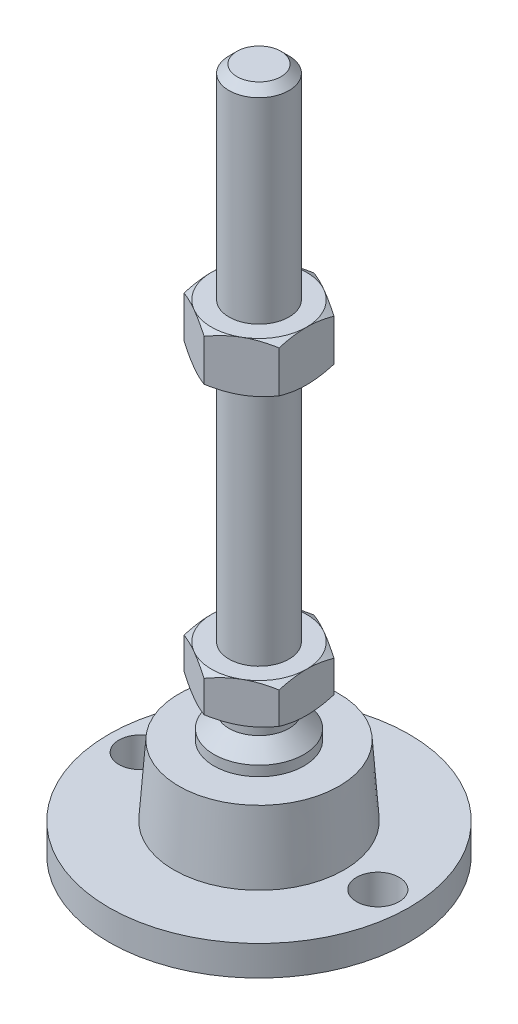
SolidWorks part; units mm, degrees
ref_plane "Спереди" through (0, 0, 0) normal (0, 0, 1) x (1, 0, 0)
ref_plane "Сверху" through (0, 0, 0) normal (0, 1, 0) x (1, 0, 0)
ref_plane "Справа" through (0, 0, 0) normal (1, 0, 0) x (0, 0, -1)
sketch "Эскиз1" plane through (0, 0, 0) normal (0, 0, 1) x (1, 0, 0)
  line L0 (0, 0) -> (-30, 0)
  line L3 (-30, 0) -> (-30, 6)
  line L12 (-6, 37) -> (-6, 135.4)
  line L13 (-6, 135.4) -> (-4.4, 137)
  line L14 (-4.4, 137) -> (0, 137)
  line L15 (0, 137) -> (0, 0) construction
  line L16 (-30, 6) -> (-17, 6)
  line L17 (0, 0) -> (0, 137)
  line L18 (0, 0) -> (0, -7.9595) construction
  line L19 (-6, 37) -> (-6, 29)
  line L21 (-9, 20) -> (-16, 20)
  line L22 (-17, 6) -> (-16, 20)
  line L23 (-9, 20) -> (-9, 22)
  line L24 (-9, 22) -> (-6, 25)
  line L25 (-6, 25) -> (-6, 29)
  line L26 (-6, 37) -> (0, 37) construction
  point P8 (-6, 86.2)
revolve "Повернуть1" add sketch "Эскиз1" angle 360 about L17
ref_plane "Плоскость2" through (0, 29, 0) normal (0, 1, 0) x (1, 0, 0)
sketch "Эскиз2" plane through (0, 29, 0) normal (0, 1, 0) x (1, 0, 0)
  line L1 (0, 10.9697) -> (-9.5, 5.4848)
  line L2 (-9.5, 5.4848) -> (-9.5, -5.4848)
  line L3 (-9.5, -5.4848) -> (0, -10.9697)
  line L4 (0, -10.9697) -> (9.5, -5.4848)
  line L5 (9.5, -5.4848) -> (9.5, 5.4848)
  line L6 (9.5, 5.4848) -> (0, 10.9697)
  circle A0 centre (0, 0) radius 9.5 construction
  dimension "D1" = 19
extrude "Бобышка-Вытянуть1" add sketch "Эскиз2" along normal up to vertex (8 mm away) up to point (-6, 37, 0)
ref_plane "Плоскость1" through (0, 86.2, 0) normal (0, 1, 0) x (1, 0, 0)
sketch "Эскиз3" plane through (0, 86.2, 0) normal (0, 1, 0) x (1, 0, 0)
  line L6 (9.5, 5.4848) -> (0, 10.9697)
  line L7 (0, 10.9697) -> (-9.5, 5.4848)
  line L8 (-9.5, 5.4848) -> (-9.5, -5.4848)
  line L9 (-9.5, -5.4848) -> (0, -10.9697)
  line L10 (0, -10.9697) -> (9.5, -5.4848)
  line L11 (9.5, -5.4848) -> (9.5, 5.4848)
  line L12 (9.5, 5.4848) -> (0, 10.9697)
  line L13 (0, 10.9697) -> (-9.5, 5.4848)
  line L14 (-9.5, 5.4848) -> (-9.5, -5.4848)
  line L15 (-9.5, -5.4848) -> (0, -10.9697)
  line L16 (0, -10.9697) -> (9.5, -5.4848)
  line L17 (9.5, -5.4848) -> (9.5, 5.4848)
  dimension "D1" = 0
extrude "Бобышка-Вытянуть2" add sketch "Эскиз3" along normal blind 10
sketch "Эскиз4" plane through (0, 0, 0) normal (0, 0, 1) x (1, 0, 0)
  line L0 (-9.5, 96.2) -> (-18.1603, 91.2)
  line L1 (-18.1603, 91.2) -> (-18.1603, 96.2)
  line L2 (-18.1603, 96.2) -> (-9.5, 96.2)
  line L3 (-18.1603, 91.2) -> (-9.5, 86.2)
  line L4 (50, 86.2) -> (-50, 86.2) construction
  line L5 (-9.5, 86.2) -> (-18.1603, 86.2)
  line L6 (-18.1603, 86.2) -> (-18.1603, 91.2)
  line L7 (-9.5, 96.2) -> (-9.5, 86.2) construction
  line L8 (-9.5, 37) -> (-16.4282, 37)
  line L9 (-16.4282, 37) -> (-16.4282, 33)
  line L10 (-16.4282, 33) -> (-9.5, 37)
  line L11 (-9.5, 29) -> (-16.4282, 33)
  line L12 (-16.4282, 33) -> (-16.4282, 29)
  line L13 (-16.4282, 29) -> (-9.5, 29)
  line L14 (0, 137) -> (0, 96.3793) construction
  line L15 (50, 29) -> (-50, 29) construction
  dimension "D1" = 30
  dimension "D2" = 30
revolve "Вырез-Повернуть2" cut sketch "Эскиз4" angle 360 about L14
sketch "Эскиз5" plane through (0, 6, 0) normal (0, 1, 0) x (1, 0, 0)
  line L0 (23.75, 0) -> (-23.75, 0) construction
  circle A0 centre (-23.75, 0) radius 4.25
  circle A1 centre (23.75, 0) radius 4.25
  circle A2 centre (0, 0) radius 30 construction
  dimension "D1" = 8.5
  dimension "D2" = 2
extrude "Вырез-Вытянуть1" cut sketch "Эскиз5" against normal through all
equation "\"D13@Эскиз1\"=\"D12@Эскиз1\"/2"
